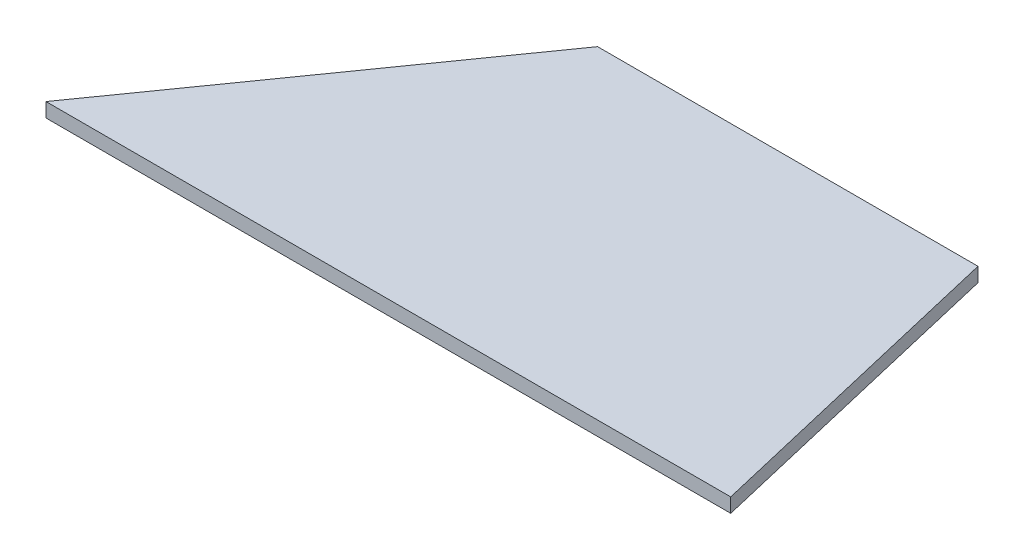
SolidWorks part; units mm, degrees
ref_plane "Front Plane" through (0, 0, 0) normal (0, 0, 1) x (1, 0, 0)
ref_plane "Top Plane" through (0, 0, 0) normal (0, 1, 0) x (1, 0, 0)
ref_plane "Right Plane" through (0, 0, 0) normal (1, 0, 0) x (0, 0, -1)
sketch "Sketch2" plane through (0, 0, 0) normal (0, 1, 0) x (1, 0, 0)
  line L3 (228.6, 0) -> (203.2, 107.95)
  line L4 (203.2, 107.95) -> (76.2, 107.95)
  line L5 (76.2, 107.95) -> (0, 0)
  line L8 (0, 0) -> (228.6, 0)
  dimension "D1" = 228.6
  dimension "D2" = 127
  dimension "D3" = 107.95
  dimension "D7" = 76.2
extrude "Boss-Extrude1" add sketch "Sketch2" along normal blind 4.7625
